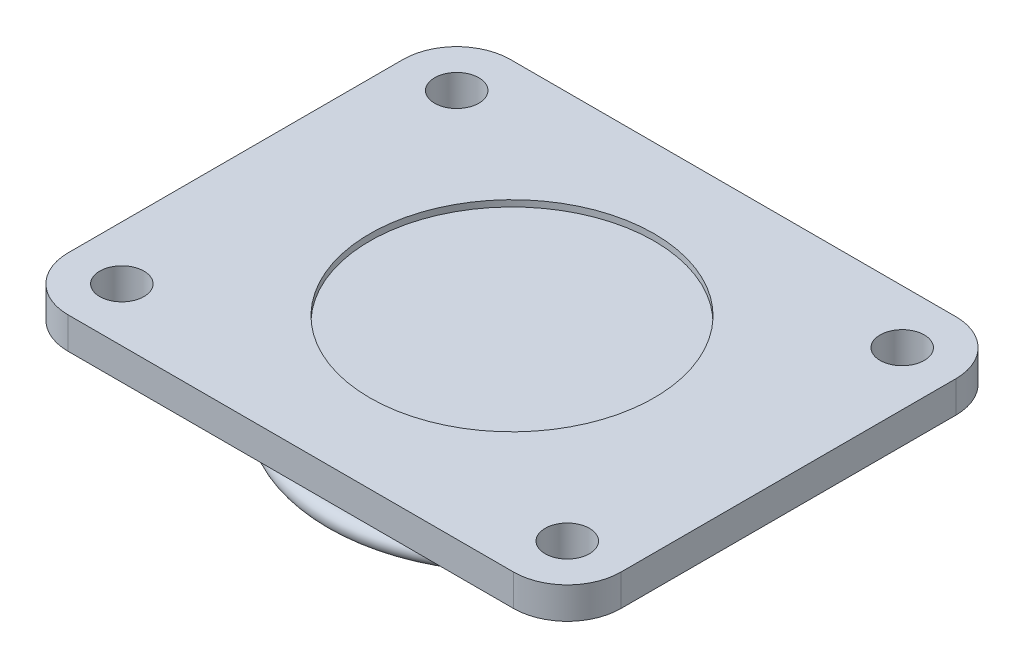
SolidWorks part; units mm, degrees
ref_plane "Front Plane" through (0, 0, 0) normal (0, 0, 1) x (1, 0, 0)
ref_plane "Top Plane" through (0, 0, 0) normal (0, 1, 0) x (1, 0, 0)
ref_plane "Right Plane" through (0, 0, 0) normal (1, 0, 0) x (0, 0, -1)
sketch "Sketch1" plane through (0, 0, 0) normal (0, 1, 0) x (1, 0, 0)
  line L1 (-70.5, 70) -> (70.5, 70)
  line L2 (-87.5, 53) -> (-87.5, -53)
  line L3 (-70.5, -70) -> (70.5, -70)
  line L4 (87.5, 53) -> (87.5, -53)
  line L5 (-87.5, 70) -> (87.5, -70) construction
  line L6 (-87.5, -70) -> (87.5, 70) construction
  arc A0 (70.5, 70) -> (87.5, 53) centre (70.5, 53) cw
  arc A1 (70.5, -70) -> (87.5, -53) centre (70.5, -53) ccw
  arc A2 (-87.5, -53) -> (-70.5, -70) centre (-70.5, -53) ccw
  arc A3 (-70.5, 70) -> (-87.5, 53) centre (-70.5, 53) ccw
  circle A4 centre (-70.5, 53) radius 7
  circle A5 centre (70.5, 53) radius 7
  circle A6 centre (70.5, -53) radius 7
  circle A7 centre (-70.5, -53) radius 7
  point P0 (0, 0)
  dimension "D3" = 17
  dimension "D4" = 14
  dimension "D1" = 175
  dimension "D2" = 140
extrude "Boss-Extrude2" add sketch "Sketch1" along normal blind 10
sketch "Sketch3" plane through (0, 0, 0) normal (0, -1, 0) x (-1, 0, 0)
  circle A0 centre (0, 0) radius 56
  dimension "D1" = 112
extrude "Boss-Extrude4" add sketch "Sketch3" along normal blind 20
sketch "Sketch4" plane through (0, 0, 0) normal (1, 0, 0) x (0, 0, -1)
  circle A0 centre (-56, -16.4604) radius 3
  dimension "D1" = 6
sketch "Sketch5" plane through (0, 0, 0) normal (1, 0, 0) x (0, 0, -1)
  line L0 (-56, 0) -> (-56, -20) construction
  line L1 (0, 0) -> (0, -30.0121) construction
  circle A0 centre (-56, -17) radius 3
  dimension "D1" = 6
revolve "Revolve1" add sketch "Sketch5" angle 360 about L1
sketch "Sketch6" plane through (0, -20, 0) normal (0, -1, 0) x (1, 0, 0)
  circle A0 centre (0, 0) radius 7.5
  dimension "D1" = 15
extrude "Boss-Extrude5" add sketch "Sketch6" along normal blind 25
cosmetic thread "Cosmetic Thread1" parameters "D2"=11.797
cosmetic thread "Cosmetic Thread2" parameters "D2"=6.619
cosmetic thread "Cosmetic Thread5" parameters "D1"=5, "D2"=11.797
chamfer "Chamfer1" distance 1 angle 45 1 edges at (0, -45, -7.5)
sketch "Sketch7" plane through (0, 10, 0) normal (0, 1, 0) x (1, 0, 0)
  circle A0 centre (0, 0) radius 45
  dimension "D1" = 90
extrude "Cut-Extrude2" cut sketch "Sketch7" against normal blind 2
